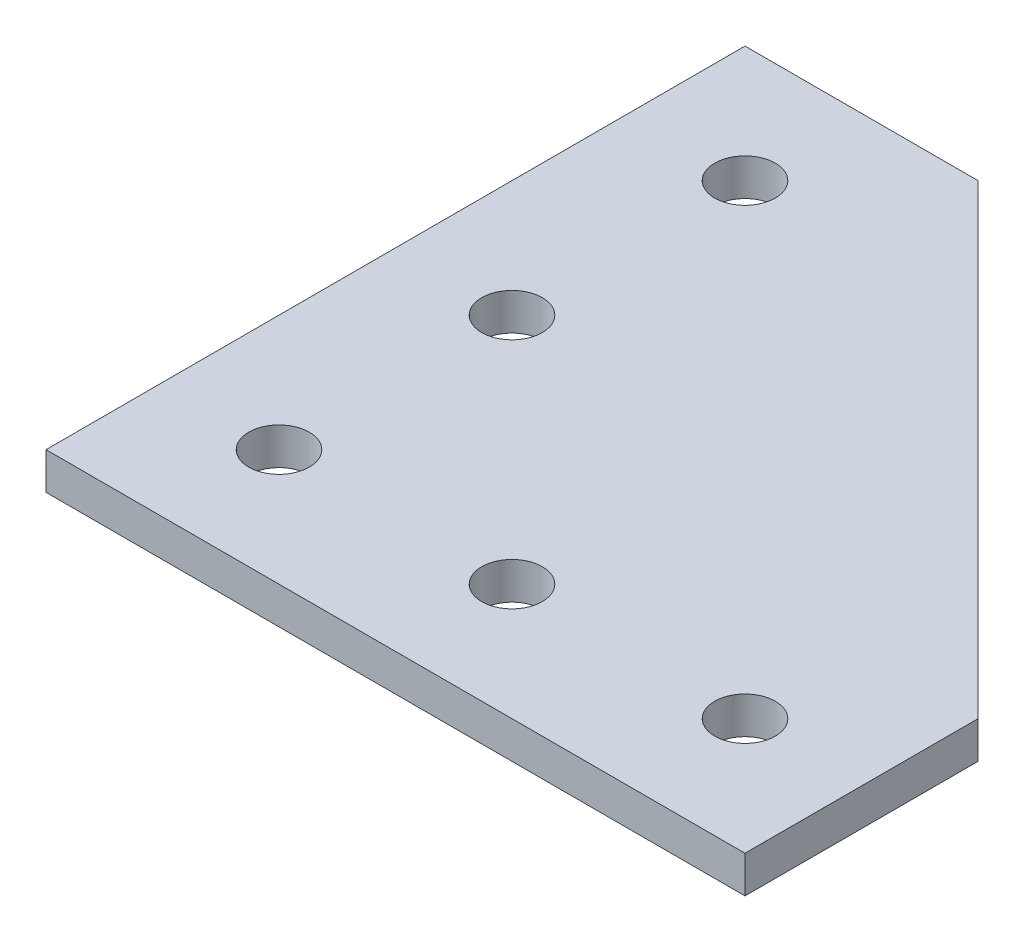
SolidWorks part; units mm, degrees
material "6061-T6 (SS)"
ref_plane "Front Plane" through (0, 0, 0) normal (0, 0, 1) x (1, 0, 0)
ref_plane "Top Plane" through (0, 0, 0) normal (0, 1, 0) x (1, 0, 0)
ref_plane "Right Plane" through (0, 0, 0) normal (1, 0, 0) x (0, 0, -1)
sketch "Sketch1" plane through (0, 0, 0) normal (0, 1, 0) x (1, 0, 0)
  line L0 (60, 0) -> (60, 20)
  line L1 (0, 0) -> (60, 0)
  line L2 (0, 0) -> (0, 60)
  line L3 (0, 60) -> (20, 60)
  line L4 (60, 20) -> (20, 60)
  line L5 (10, 10) -> (50, 10) construction
  line L6 (10, 50) -> (10, 10) construction
  circle A0 centre (50, 10) radius 2.6
  circle A1 centre (10, 50) radius 2.6
  circle A2 centre (30, 10) radius 2.6
  circle A3 centre (10, 10) radius 2.6
  circle A4 centre (10, 30) radius 2.6
  dimension "D5" = 5.2
  dimension "D6" = 40
  dimension "D9" = 40
  dimension "D8" = 10
  dimension "D1" = 60
  dimension "D2" = 60
  dimension "D3" = 20
  dimension "D4" = 20
  dimension "D7" = 10
extrude "Boss-Extrude1" add sketch "Sketch1" along normal blind 3.175
equation "\"D8@Sketch1\"=\"D7@Sketch1\""
equation "\"D9@Sketch1\"=\"D6@Sketch1\""
equation "\"D2@Sketch1\"=\"D1@Sketch1\""
equation "\"D4@Sketch1\"=\"D3@Sketch1\""
